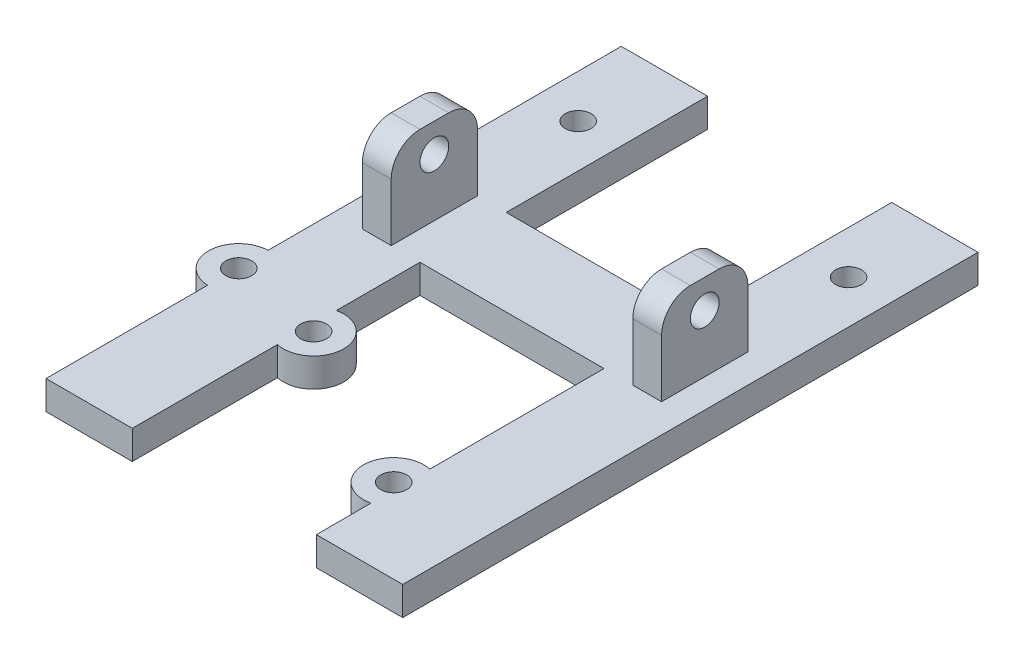
SolidWorks part; units mm, degrees
ref_plane "Front Plane" through (0, 0, 0) normal (0, 0, 1) x (1, 0, 0)
ref_plane "Top Plane" through (0, 0, 0) normal (0, 1, 0) x (1, 0, 0)
ref_plane "Right Plane" through (0, 0, 0) normal (1, 0, 0) x (0, 0, -1)
sketch "Sketch1" plane through (0, 0, 0) normal (0, 1, 0) x (1, 0, 0)
  line L0 (0, 0) -> (0, 100)
  line L1 (0, 100) -> (15, 100)
  line L2 (15, 100) -> (15, 0)
  line L3 (15, 0) -> (0, 0)
  line L4 (47, 100) -> (47, 0)
  line L5 (47, 0) -> (62, 0)
  line L6 (62, 0) -> (62, 100)
  line L7 (62, 100) -> (47, 100)
  line L8 (15, 50) -> (47, 50)
  line L9 (15, 65) -> (47, 65)
  line L10 (15, 65) -> (15, 50)
  line L11 (47, 65) -> (47, 50)
  dimension "D1" = 15
  dimension "D2" = 100
  dimension "D3" = 62
  dimension "D5" = 50
  dimension "D4" = 15
extrude "Boss-Extrude1" add sketch "Sketch1" along normal mid plane 5 contours L3 L2 L1 L0 | L9 L2 L8 L4 | L6 L7 L4 L5
sketch "Sketch2" plane through (0, 2.5, 0) normal (0, 1, 0) x (1, 0, 0)
  line L0 (31, 65) -> (31, 50) construction
  line L1 (15, 65) -> (47, 65) construction
  line L2 (15, 50) -> (47, 50) construction
  line L3 (52, 65) -> (52, 50)
  line L4 (52, 50) -> (57, 50)
  line L5 (57, 50) -> (57, 65)
  line L6 (57, 65) -> (52, 65)
  line L7 (5, 65) -> (5, 50)
  line L8 (5, 50) -> (10, 50)
  line L9 (10, 50) -> (10, 65)
  line L10 (10, 65) -> (5, 65)
  line L11 (10, 65) -> (52, 65) construction
  point P12 (31, 65)
  dimension "D1" = 5
  dimension "D2" = 42
extrude "Boss-Extrude2" add sketch "Sketch2" along normal blind 15
sketch "Sketch3" plane through (5, 0, 0) normal (-1, 0, 0) x (0, 0, 1)
  line L0 (-65, 17.5) -> (-50, 17.5) construction
  circle A0 centre (-57.5, 12.5) radius 2.5
  point P5 (-57.5, 17.5)
  dimension "D2" = 5
  dimension "D1" = 5
extrude "Cut-Extrude1" cut sketch "Sketch3" against normal up to surface (52 mm away) up to face at (57, 10, -57.5)
fillet "Fillet2" radius 5 4 edges at (54.5, 17.5, -50) (54.5, 17.5, -65) (7.5, 17.5, -65) (7.5, 17.5, -50)
sketch "Sketch4" plane through (0, 2.5, 0) normal (0, 1, 0) x (1, 0, 0)
  line L0 (47, 16.5279) -> (47, 19.7211)
  line L1 (47, 50) -> (47, 0) construction
  line L2 (47, 12.6747) -> (47, 9.4816)
  line L3 (15, 35.4716) -> (15, 32.2792)
  line L4 (15, 50) -> (15, 0) construction
  line L5 (15, 28.4234) -> (15, 25.2311)
  line L6 (0, 38.5989) -> (0, 35.5956)
  line L7 (0, 0) -> (0, 100) construction
  line L8 (0, 31.107) -> (0, 28.1038)
  circle A0 centre (45.8378, 14.6013) radius 2.25
  circle A1 centre (16.16, 30.3513) radius 2.25
  circle A2 centre (0.16, 33.3513) radius 2.25
  arc A3 (47, 19.7211) -> (47, 9.4816) centre (45.8378, 14.6013) ccw
  arc A4 (15, 25.2311) -> (15, 35.4716) centre (16.16, 30.3513) ccw
  arc A5 (0, 38.5989) -> (0, 28.1038) centre (0.16, 33.3513) ccw
  circle A7 centre (0.16, 33.3513) radius 5.25 construction
  circle A8 centre (16.16, 30.3513) radius 5.25 construction
  circle A9 centre (45.8378, 14.6013) radius 5.25 construction
  point P12 (51.0878, 14.6013)
  point P14 (21.41, 30.3513)
  point P33 (5.41, 33.3513)
  line M2 (15, 0) -> (15, 50)
  line M4 (47, 50) -> (47, 0)
  line M12 (0, 100) -> (0, 0)
  dimension "D1" = 3
extrude "Boss-Extrude3" add sketch "Sketch4" against normal up to surface (5 mm away) contours A3 A0 M4 | A4 A1 M2 | A5 A2 M12
sketch "Sketch5" plane through (0, 2.5, 0) normal (0, 1, 0) x (1, 0, 0)
  circle A0 centre (0.16, 33.3513) radius 2.25
  circle A1 centre (16.16, 30.3513) radius 2.25
  circle A2 centre (45.8378, 14.6013) radius 2.25
extrude "Cut-Extrude3" cut sketch "Sketch5" against normal up to surface (5 mm away)
sketch "Sketch6" plane through (0, 2.5, 0) normal (0, 1, 0) x (1, 0, 0)
  line L0 (0, 100) -> (15, 100) construction
  line L1 (5, 65) -> (10, 65) construction
  line L3 (62, 100) -> (47, 100) construction
  line L4 (52, 65) -> (57, 65) construction
  circle A0 centre (7.5, 85) radius 2.25
  circle A1 centre (54.5, 85) radius 2.25
  point P4 (7.5, 100)
  point P11 (54.5, 100)
  dimension "D1" = 4.5
  dimension "D2" = 20
  dimension "D3" = 4.5
  dimension "D4" = 20
extrude "Cut-Extrude4" cut sketch "Sketch6" against normal blind 5
